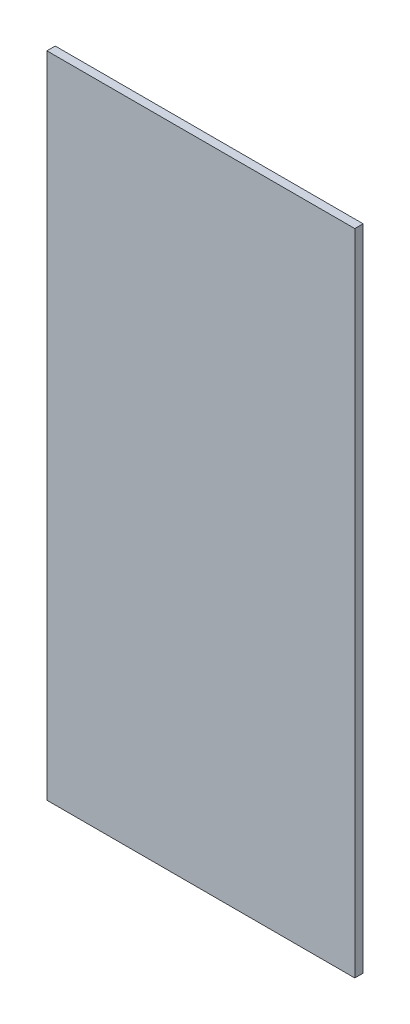
SolidWorks part; units mm, degrees
ref_plane "Alzado" through (0, 0, 0) normal (0, 0, 1) x (1, 0, 0)
ref_plane "Planta" through (0, 0, 0) normal (0, 1, 0) x (1, 0, 0)
ref_plane "Vista lateral" through (0, 0, 0) normal (1, 0, 0) x (0, 0, -1)
sketch "Croquis2" plane through (0, 0, 0) normal (0, 1, 0) x (1, 0, 0)
  line L1 (-117.475, 3.175) -> (117.475, 3.175)
  line L2 (-117.475, 3.175) -> (-117.475, -3.175)
  line L3 (-117.475, -3.175) -> (117.475, -3.175)
  line L4 (117.475, 3.175) -> (117.475, -3.175)
  line L5 (-117.475, 3.175) -> (117.475, -3.175) construction
  line L6 (-117.475, -3.175) -> (117.475, 3.175) construction
  point P0 (0, 0)
  dimension "D1" = 234.95
  dimension "D2" = 6.35
extrude "Saliente-Extruir1" add sketch "Croquis2" along normal blind 495.3
